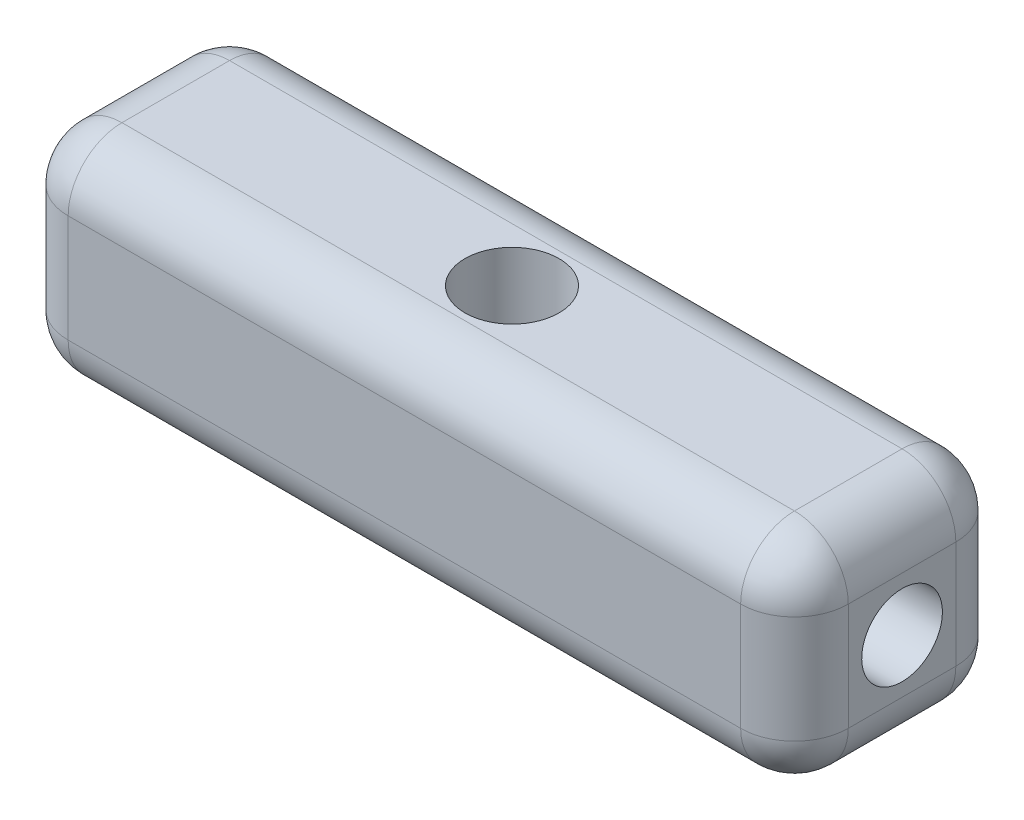
SolidWorks part; units mm, degrees
ref_plane "Alzado" through (0, 0, 0) normal (0, 0, 1) x (1, 0, 0)
ref_plane "Planta" through (0, 0, 0) normal (0, 1, 0) x (1, 0, 0)
ref_plane "Vista lateral" through (0, 0, 0) normal (1, 0, 0) x (0, 0, -1)
sketch "Croquis1" plane through (0, 0, 0) normal (0, 0, 1) x (1, 0, 0)
  line L1 (0, 0) -> (29, 0)
  line L2 (0, 0) -> (0, 8)
  line L3 (0, 8) -> (29, 8)
  line L4 (29, 0) -> (29, 8)
  dimension "D1" = 8
  dimension "D2" = 29
extrude "Saliente-Extruir1" add sketch "Croquis1" along normal blind 8
sketch "Croquis4" plane through (0, 8, 0) normal (0, 1, 0) x (1, 0, 0)
  line L0 (29, -8) -> (29, 0) construction
  line L1 (29, 0) -> (0, 0) construction
  circle A0 centre (14.5, -4) radius 1.75
  dimension "D1" = 3.5
  dimension "D2" = 14.5
  dimension "D3" = 4
extrude "Cortar-Extruir1" cut sketch "Croquis4" against normal through all
fillet "Redondeo1" radius 2 12 edges at (14.5, 0, 0) (14.5, 0, 8) (14.5, 8, 0) (14.5, 8, 8) (29, 0, 4) (29, 4, 8) (29, 8, 4) (29, 4, 0) (0, 0, 4) (0, 4, 8) (0, 8, 4) (0, 4, 0)
sketch "Croquis5" plane through (29, 0, 0) normal (1, 0, 0) x (0, 0, -1)
  line L0 (-6, 0) -> (-2, 0) construction
  line L1 (0, 2) -> (0, 6) construction
  circle A0 centre (-4, 4) radius 1.5
  dimension "D1" = 3
  dimension "D2" = 4
  dimension "D3" = 4
extrude "Cortar-Extruir2" cut sketch "Croquis5" against normal blind 9.5
sketch "Croquis6" plane through (0, 0, 0) normal (-1, 0, 0) x (0, 0, 1)
  line L0 (6, 0) -> (2, 0) construction
  line L1 (8, 6) -> (8, 2) construction
  circle A0 centre (4, 4) radius 1.5
  dimension "D1" = 3
  dimension "D2" = 4
  dimension "D3" = 4
extrude "Cortar-Extruir3" cut sketch "Croquis6" against normal blind 9.5
